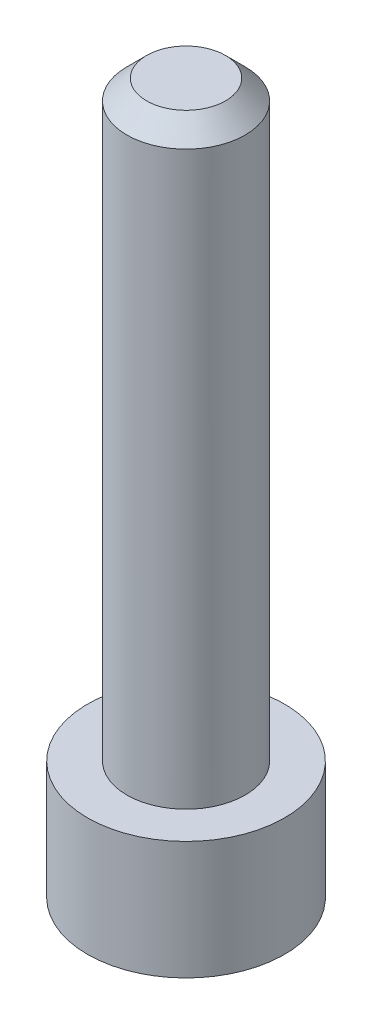
SolidWorks part; units mm, degrees
ref_plane "Plan de face" through (0, 0, 0) normal (0, 0, 1) x (1, 0, 0)
ref_plane "Plan de dessus" through (0, 0, 0) normal (0, 1, 0) x (1, 0, 0)
ref_plane "Plan de droite" through (0, 0, 0) normal (1, 0, 0) x (0, 0, -1)
sketch "Esquisse1" plane through (0, 0, 0) normal (0, 0, 1) x (1, 0, 0)
  line L0 (0, 0) -> (1.5, 0)
  line L1 (1.5, 0) -> (1.5, -15)
  line L2 (1.5, -15) -> (2.5, -15)
  line L3 (2.5, -15) -> (2.5, -18)
  line L4 (2.5, -18) -> (0, -18)
  line L5 (0, 0) -> (0, -4.6949) construction
  line L6 (0, 0) -> (0, -18)
revolve "Révolution1" add sketch "Esquisse1" angle 360 about L5
chamfer "Chanfrein1" distance 0.5 angle 45 1 edges at (0, 0, 1.5)
